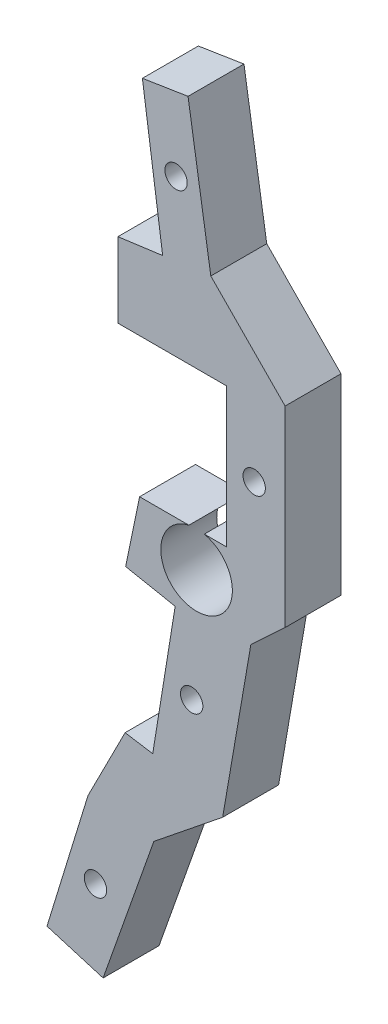
SolidWorks part; units mm, degrees
material "PMMA"
ref_plane "Front Plane" through (0, 0, 0) normal (0, 0, 1) x (1, 0, 0)
ref_plane "Top Plane" through (0, 0, 0) normal (0, 1, 0) x (1, 0, 0)
ref_plane "Right Plane" through (0, 0, 0) normal (1, 0, 0) x (0, 0, -1)
sketch "Sketch1" plane through (0, 0, 0) normal (0, 0, 1) x (1, 0, 0)
  line L0 (-30.345, 29.355) -> (-26.2648, 29.999)
  line L1 (-26.2648, 29.999) -> (-24.2299, 17.1058)
  line L2 (-24.2299, 17.1058) -> (-17.5894, 10.3557)
  line L3 (-17.5894, 10.3557) -> (-17.5894, -6.796)
  line L4 (-17.5894, -6.796) -> (-20.6482, -9.6321)
  line L5 (-20.6482, -9.6321) -> (-23.1692, -24.2713)
  line L6 (-23.1692, -24.2713) -> (-29.3228, -29.2184)
  line L7 (-29.3228, -29.2184) -> (-33.8583, -42.0616)
  line L8 (-33.8583, -42.0616) -> (-38.8752, -40.5573)
  line L9 (-38.8752, -40.5573) -> (-35.2108, -28.6128)
  line L10 (-35.2108, -28.6128) -> (-31.8905, -22.0823)
  line L11 (-31.8905, -22.0823) -> (-29.4225, -22.4809)
  line L12 (-29.4225, -22.4809) -> (-27.4169, -10.0626)
  line L13 (-27.4169, -10.0626) -> (-31.846, -9.1978)
  line L14 (-31.846, -9.1978) -> (-30.5966, -3.1687)
  line L15 (-30.5966, -3.1687) -> (-22.846, -3.1687)
  line L16 (-22.846, -3.1687) -> (-22.846, 9.3)
  line L17 (-22.846, 9.3) -> (-32.5343, 9.3)
  line L18 (-32.5343, 9.3) -> (-32.5343, 15.9983)
  line L19 (-32.5343, 15.9983) -> (-28.5335, 16.5375)
  line L20 (-28.5335, 16.5375) -> (-30.345, 29.355)
  line L21 (-54.3357, 25.8419) -> (-30.311, 29.36) construction
  circle A0 centre (-27.3351, 23.2554) radius 1
  circle A1 centre (-20.35, 3.1) radius 1
  circle A2 centre (-25.9416, -16.5673) radius 1
  circle A3 centre (-34.541, -35.1178) radius 1
  dimension "D1" = 2
  dimension "D2" = 2
  dimension "D3" = 2
  dimension "D4" = 2
extrude "Boss-Extrude1" add sketch "Sketch1" along normal blind 5
sketch "Sketch2" plane through (0, 0, 0) normal (0, 0, -1) x (-1, 0, 0)
  circle A0 centre (25.5, -6.2934) radius 3.2
extrude "Cut-Extrude1" cut sketch "Sketch2" against normal through all
